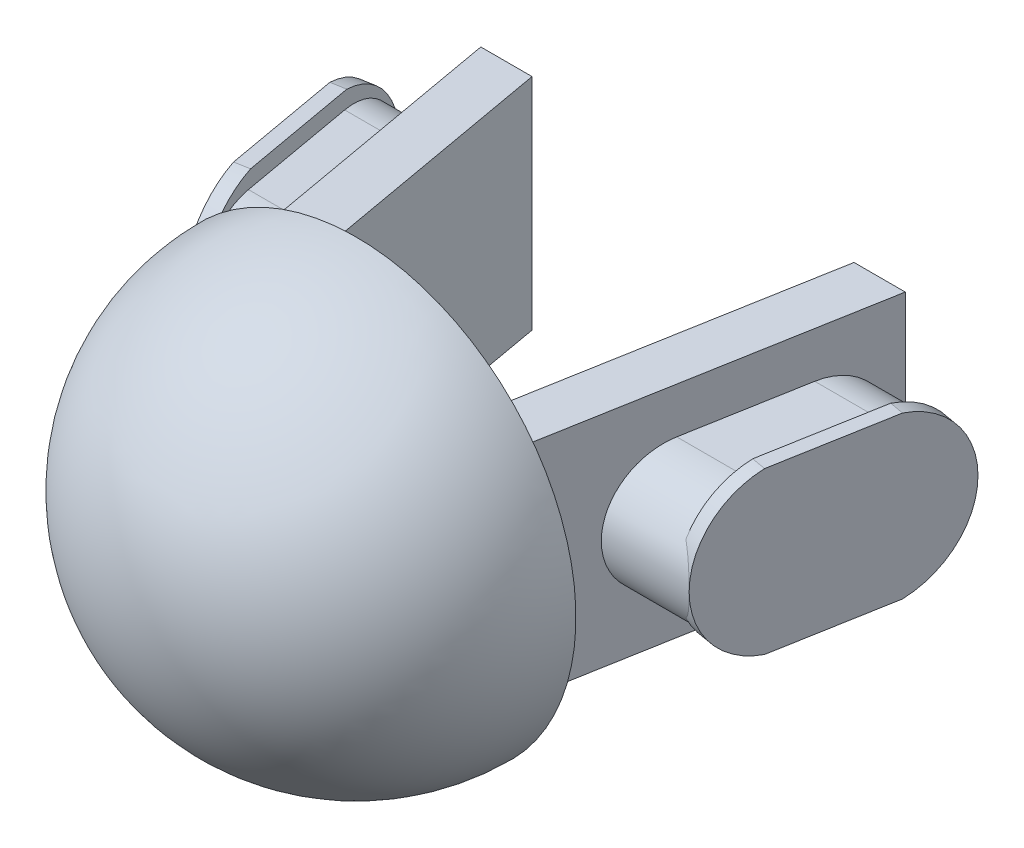
SolidWorks part; units mm, degrees
material "ABS"
ref_plane "Front Plane" through (0, 0, 0) normal (1, 0, 0) x (0, 1, 0)
ref_plane "Top Plane" through (0, 0, 0) normal (0, 0, 1) x (0, 1, 0)
ref_plane "Right Plane" through (0, 0, 0) normal (0, 1, 0) x (-1, 0, 0)
sketch "Sketch4" plane through (0, 0, 0) normal (0, 0, 1) x (0, 1, 0)
  line L1 (-3.5, -3.5) -> (3.5, -3.5)
  line L2 (-3.5, -3.5) -> (-3.5, 3.5)
  line L3 (-3.5, 3.5) -> (3.5, 3.5)
  line L4 (3.5, -3.5) -> (3.5, 3.5)
  line L5 (0, 3.5) -> (0, -3.5) construction
  line L6 (-3.5, 0) -> (3.5, 0) construction
  point P0 (0, 0)
  dimension "D1" = 7
extrude "Boss-Extrude2" add sketch "Sketch4" along normal blind 2.55
sketch "Sketch5" plane through (0, 0, 2.55) normal (0, 0, 1) x (1, 0, 0)
  line L0 (0, -1000) -> (0, 49000) construction
  line L1 (0, 15) -> (0, -15)
  arc A0 (0, -15) -> (0, 15) centre (0, 0) ccw
  dimension "D1" = 30
revolve "Revolve1" add sketch "Sketch5" angle 180 about L0
sketch "Sketch2" plane through (0, 0, 0) normal (0, 0, 1) x (0, 1, 0)
  line L1 (-1.85, -1.85) -> (1.85, -1.85)
  line L2 (-1.85, -1.85) -> (-1.85, 1.85)
  line L3 (-1.85, 1.85) -> (1.85, 1.85)
  line L4 (1.85, -1.85) -> (1.85, 1.85)
  line L5 (0, 1.85) -> (0, -1.85) construction
  line L6 (-1.85, 0) -> (1.85, 0) construction
  line L11 (0, 4.85) -> (0, -4.85) construction
  line L12 (-4.85, 0) -> (4.85, 0) construction
  line L17 (0, 4.7521) -> (0, -4.7521) construction
  line L18 (-3.4537, 0) -> (3.4537, 0) construction
  point P0 (0, 0)
  point P4 (0, 0)
  point P5 (0, 0)
  dimension "D1" = 3.7
extrude "Cut-Extrude1" cut sketch "Sketch2" along normal blind 1.5
sketch "Sketch13" plane through (0, 0, 0) normal (0, 1, 0) x (-1, 0, 0)
  line L0 (-6.9, 2.55) -> (-10.9969, -20.45)
  line L1 (-6.9, 2.55) -> (-10.4, 2.55)
  line L2 (-10.9969, -20.45) -> (-14.4969, -20.45)
  line L3 (-10.4, 2.55) -> (-14.4969, -20.45)
  line L4 (0, -1000) -> (0, 49000) construction
  line L5 (-3.5, 0) -> (3.5, 0) construction
  line L6 (-15, -996) -> (-15, 49004) construction
  line L7 (-15, 2.55) -> (15, 2.55) construction
  line L8 (10.9969, -20.45) -> (14.4969, -20.45)
  line L9 (10.4, 2.55) -> (14.4969, -20.45)
  line L10 (6.9, 2.55) -> (10.4, 2.55)
  line L11 (6.9, 2.55) -> (10.9969, -20.45)
  arc A0 (15, 2.55) -> (-15, 2.55) centre (0, 2.55) ccw construction
  point P10 (0, 0)
  dimension "D1" = 10.1
  dimension "D2" = 3.5
  dimension "D3" = 4.6
  dimension "D4" = 23
extrude "Boss-Extrude6" add sketch "Sketch13" along normal mid plane 15
sketch "Sketch14" plane through (0, 0, 0) normal (1, 0, 0) x (0, 1, 0)
  line L0 (0, -7.2) -> (0, -15.2) construction
  line L1 (4.375, -7.2) -> (4.375, -15.2)
  line L2 (-4.375, -7.2) -> (-4.375, -15.2)
  line L3 (-15, 2.55) -> (15, 2.55) construction
  arc A0 (4.375, -7.2) -> (-4.375, -7.2) centre (0, -7.2) ccw
  arc A1 (-4.375, -15.2) -> (4.375, -15.2) centre (0, -15.2) ccw
  point P3 (0, -11.2)
  dimension "D2" = 4.375
  dimension "D1" = 9.75
  dimension "D3" = 8
extrude "Boss-Extrude7" add sketch "Sketch14" along normal mid plane 45 contours L2 A1 L1 A0
sketch "Sketch15" plane through (0, 0, 0) normal (0, 1, 0) x (-1, 0, 0)
  line L0 (-7.8574, -2.825) -> (7.8574, -2.825)
  line L1 (7.8574, -2.825) -> (10.9969, -20.45)
  line L2 (10.9969, -20.45) -> (-10.9969, -20.45)
  line L3 (-10.9969, -20.45) -> (-7.8574, -2.825)
  line L4 (-17.3574, -2.825) -> (-20.3411, -19.575)
  line L6 (-22.5, -19.575) -> (-14.3411, -19.575) construction
  line L7 (-20.3411, -19.575) -> (-22.5, -19.575)
  line L8 (-22.5, -19.575) -> (-22.5, -2.825)
  line L9 (-22.5, -2.825) -> (-17.3574, -2.825)
  line L10 (-10.4, 2.55) -> (-14.4969, -20.45) construction
  line L11 (0, -1000) -> (0, 49000) construction
  line L12 (20.3411, -19.575) -> (22.5, -19.575)
  line L13 (22.5, -19.575) -> (22.5, -2.825)
  line L14 (22.5, -2.825) -> (17.3574, -2.825)
  line L15 (17.3574, -2.825) -> (20.3411, -19.575)
  dimension "D1" = 6
extrude "Cut-Extrude2" cut sketch "Sketch15" against normal mid plane 45
sketch "Sketch16" plane through (-16.3359, 0, 2.9099) normal (-0.9845, 0, 0.1754) x (0, -1, 0)
  line L0 (0, -10.269) -> (0, -18.3949) construction
  line L1 (5.5, -10.269) -> (5.5, -18.3949)
  line L2 (-5.5, -10.269) -> (-5.5, -18.3949)
  line L3 (-1000, -14.332) -> (49000, -14.332) construction
  arc A0 (5.5, -10.269) -> (-5.5, -10.269) centre (0, -10.269) ccw construction
  arc A1 (-5.5, -18.3949) -> (5.5, -18.3949) centre (0, -18.3949) ccw construction
  arc A2 (5.5, -10.269) -> (-5.5, -10.269) centre (0, -11.4506) ccw
  arc A3 (5.5, -18.3949) -> (-5.5, -18.3949) centre (0, -17.2133) cw
  ellipse E0 centre (0, -10.269) end of major axis (0, -14.7129) minor radius 4.375 (4.375, -10.269) -> (-4.375, -10.269) ccw construction
  ellipse E1 centre (0, -18.3949) end of major axis (0, -22.8388) minor radius 4.375 (-4.375, -18.3949) -> (4.375, -18.3949) ccw construction
  point P3 (0, -14.332)
  dimension "D1" = 5.5
  dimension "D2" = 11.251
  dimension "D3" = 8.1259
  dimension "D4" = 11
extrude "Boss-Extrude8" add sketch "Sketch16" against normal blind 1
mirror "Mirror1" about plane through (0, 0, 0) normal (1, 0, 0) of "Boss-Extrude8"
